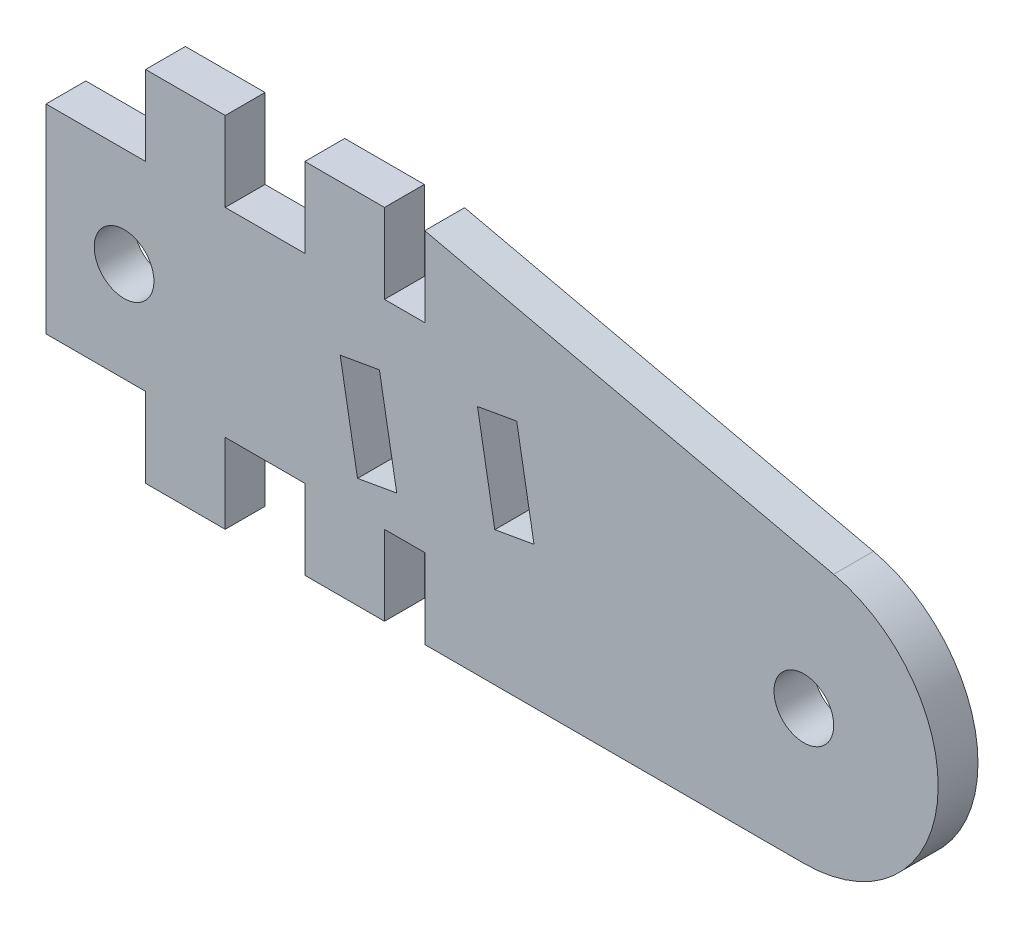
SolidWorks part; units mm, degrees
ref_plane "Front Plane" through (0, 0, 0) normal (0, 0, 1) x (1, 0, 0)
ref_plane "Top Plane" through (0, 0, 0) normal (0, 1, 0) x (1, 0, 0)
ref_plane "Right Plane" through (0, 0, 0) normal (1, 0, 0) x (0, 0, -1)
sketch "Sketch1" plane through (0, 0, 0) normal (0, 0, 1) x (1, 0, 0)
  line L0 (5, 0) -> (9, 0)
  line L1 (5, 4) -> (5, 0)
  line L2 (5, 14) -> (0, 14)
  line L3 (9, 4) -> (13, 4)
  line L4 (13, 4) -> (13, 0)
  line L5 (9, 0) -> (9, 4)
  line L6 (13, 0) -> (17, 0)
  line L7 (17, 0) -> (17, 4)
  line L8 (17, 4) -> (19.0216, 4)
  line L9 (0, 14) -> (0, 4)
  line L10 (19.0216, 4) -> (19.0216, 0)
  line L11 (17, 14) -> (19.0216, 14)
  line L12 (17, 18) -> (17, 14)
  line L13 (13, 18) -> (17, 18)
  line L14 (9, 18) -> (9, 14)
  line L15 (13, 14) -> (13, 18)
  line L16 (9, 14) -> (13, 14)
  line L17 (0, 4) -> (5, 4)
  line L18 (5, 14) -> (5, 18)
  line L19 (5, 18) -> (9, 18)
  line L20 (19.0216, 0) -> (38.0595, 0)
  line L21 (27.99, 0) -> (27.99, -6.4753) construction
  line L22 (19.0216, 14) -> (19.0216, 18)
  line L23 (19.0216, 18) -> (39.5576, 13.3222)
  line L27 (23.6391, 12.0249) -> (21.6695, 11.6776)
  line L32 (16.7455, 10.8093) -> (17.6137, 5.8853)
  line L33 (16.7455, 10.8093) -> (14.7759, 10.462)
  line L34 (14.7759, 10.462) -> (15.6441, 5.538)
  line L35 (15.6441, 5.538) -> (17.6137, 5.8853)
  line L36 (21.6695, 11.6776) -> (22.5378, 6.7535)
  line L37 (22.5378, 6.7535) -> (24.5074, 7.1008)
  line L38 (23.6391, 12.0249) -> (24.5074, 7.1008)
  arc A0 (38.0595, 0) -> (39.5576, 13.3222) centre (38.0595, 6.7453) ccw
  circle A1 centre (3.9205, 9) radius 1.5
  circle A2 centre (38.0595, 6.7453) radius 12.12 construction
  circle A4 centre (38.0595, 6.7453) radius 1.5
  dimension "D16" = 9
  dimension "D13" = 5.8853
  dimension "D1" = 3
  dimension "D2" = 6.7453
  dimension "D7" = 24.24
  dimension "D3" = 3.9205
  dimension "D4" = 14.7759
  dimension "D5" = 15.6441
  dimension "D6" = 16.7455
  dimension "D8" = 21.6695
  dimension "D9" = 9
  dimension "D10" = 18
  dimension "D11" = 19.0216
  dimension "D12" = 5.538
  dimension "ThumbLinkLengthMCP" = 18.99
extrude "Boss-Extrude1" add sketch "Sketch1" along normal blind 2
equation "\"ThumbLinkLengthMCP@Sketch1\"= \"HB@parametersSketch@prostheticParameters.SLDPRT\" * 0.211"
